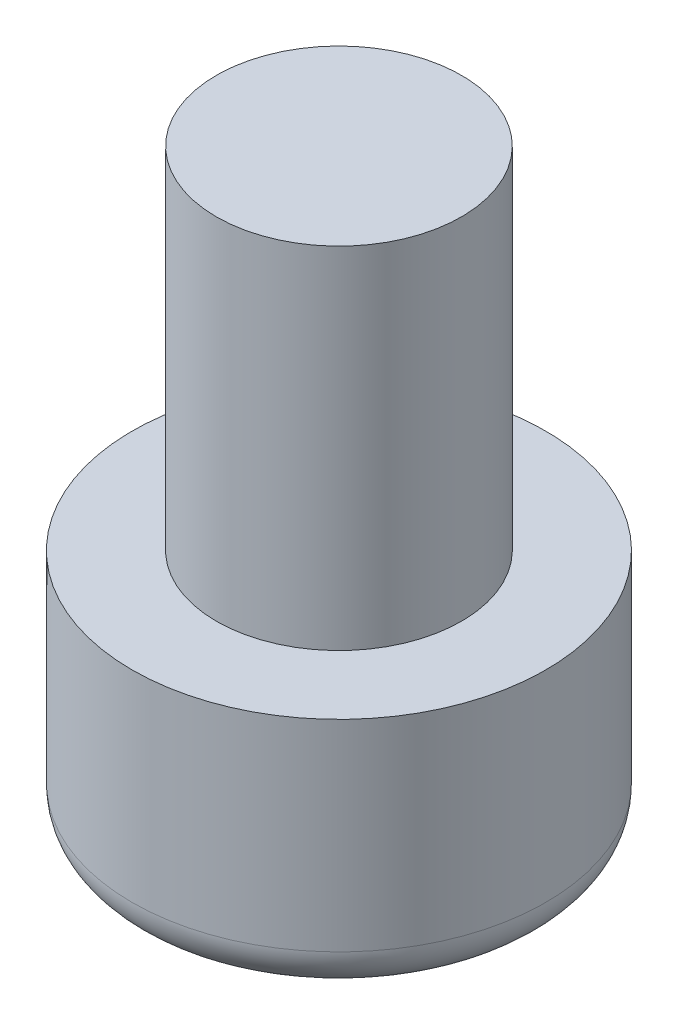
SolidWorks part; units mm, degrees
ref_plane "Front Plane" through (0, 0, 0) normal (0, 0, 1) x (1, 0, 0)
ref_plane "Top Plane" through (0, 0, 0) normal (0, 1, 0) x (1, 0, 0)
ref_plane "Right Plane" through (0, 0, 0) normal (1, 0, 0) x (0, 0, -1)
sketch "Bearing Plug" plane through (0, 0, 0) normal (0, 1, 0) x (1, 0, 0)
  circle A0 centre (0, 0) radius 4.725
  dimension "D1" = 9.45
extrude "BearingPlug Extrude" add sketch "Bearing Plug" along normal blind 5.6
sketch "Sketch2" plane through (0, 5.6, 0) normal (0, 1, 0) x (1, 0, 0)
  circle A0 centre (0, 0) radius 2.8
  dimension "D1" = 5.6
extrude "Boss-Extrude2" add sketch "Sketch2" along normal blind 8
fillet "Fillet1" radius 1 1 edges at (0, 0, 4.725)
equation "\"BearingPlugDiameter\"= 9.45mm"
equation "\"WormGearPlugDiameter\"= 5.6mm"
equation "\"BearingPlugDepth\"= 5.6mm"
equation "\"ShaftPlugDepth\"= 8mm"
equation "\"D1@Bearing Plug\"= \"BearingPlugDiameter\""
equation "\"D1@BearingPlug Extrude\"= \"BearingPlugDepth\""
equation "\"WormGearPlugDepth\"=5.75"
equation "\"D1@Boss-Extrude2\"= \"ShaftPlugDepth\""
equation "\"D1@Sketch2\"= \"WormGearPlugDiameter\""
